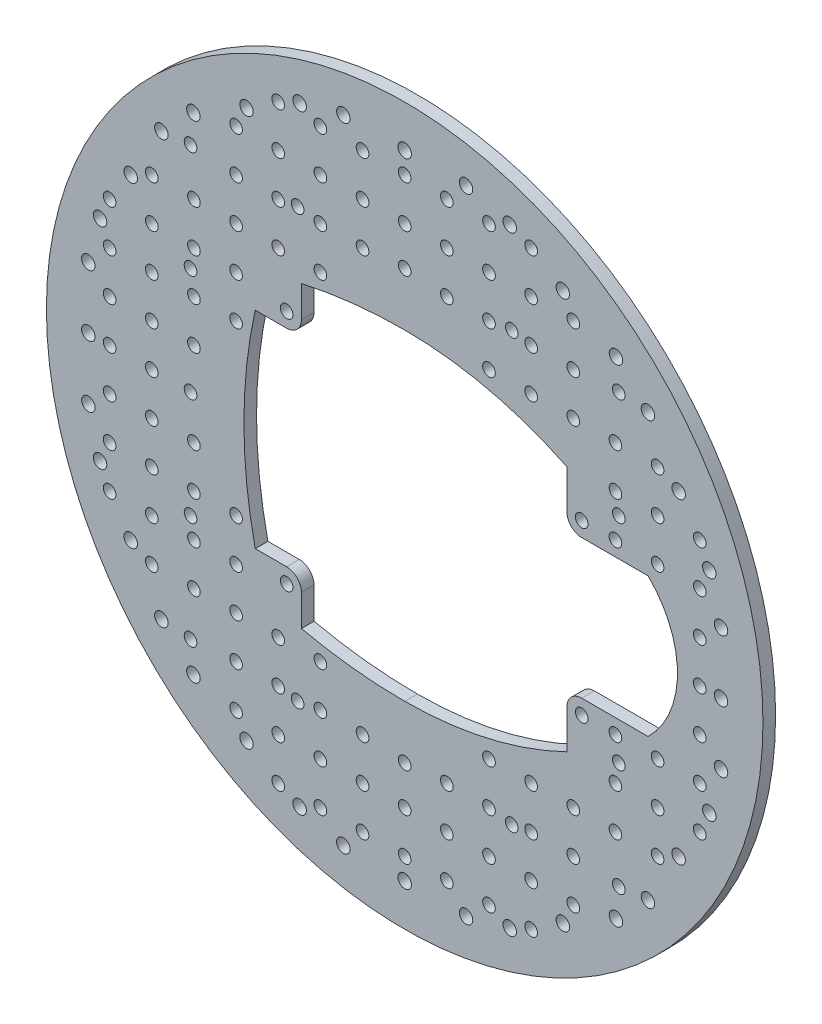
SolidWorks part; units mm, degrees
material "ABS"
ref_plane "Спереди" through (0, 0, 0) normal (0, 0, 1) x (1, 0, 0)
ref_plane "Сверху" through (0, 0, 0) normal (0, 1, 0) x (1, 0, 0)
ref_plane "Справа" through (0, 0, 0) normal (1, 0, 0) x (0, 0, -1)
sketch "Model" plane through (0, 0, 0) normal (0, 0, 1) x (1, 0, 0)
  line L0 (0, 0) -> (0, -87) construction
  line L1 (0, 0) -> (0, 87) construction
  line L2 (0, 0) -> (87, 0) construction
  line L3 (0, 0) -> (-87, 0) construction
  line L4 (38.5, 20) -> (38.5, 29.277)
  line L5 (42, 16.5) -> (57.7426, 16.5)
  line L6 (-24.5, 28) -> (-24.5, 35.4475)
  line L7 (-28, 24.5) -> (-35.4475, 24.5)
  line L8 (38.5, -20) -> (38.5, -29.277)
  line L9 (42, -16.5) -> (57.7426, -16.5)
  line L10 (-24.5, -28) -> (-24.5, -35.4475)
  line L11 (-28, -24.5) -> (-35.4475, -24.5)
  circle A295 centre (37.525, 64.9952) radius 1.6
  circle A296 centre (-50.1257, -57.7202) radius 1.6
  circle A297 centre (-57.7202, 50.1257) radius 1.6
  circle A298 centre (-24.9243, 72.2702) radius 1.6
  circle A299 centre (-75.05, 0) radius 1.6
  circle A300 centre (50.1257, -57.7202) radius 1.6
  circle A301 centre (-72.2702, 24.9243) radius 1.6
  circle A302 centre (64.9952, -37.525) radius 1.6
  circle A303 centre (50.1257, 57.7202) radius 1.6
  circle A304 centre (37.525, -64.9952) radius 1.6
  circle A305 centre (-14.55, 75.05) radius 1.6
  circle A306 centre (-72.2702, -24.9243) radius 1.6
  circle A307 centre (24.9243, -72.2702) radius 1.6
  circle A308 centre (14.55, -75.05) radius 1.6
  circle A309 centre (64.9952, 37.525) radius 1.6
  circle A310 centre (-37.525, -64.9952) radius 1.6
  circle A311 centre (-75.05, 14.55) radius 1.6
  circle A312 centre (72.2702, 24.9243) radius 1.6
  circle A313 centre (0, -75.05) radius 1.6
  circle A314 centre (-75.05, -14.55) radius 1.6
  circle A315 centre (-64.9952, 37.525) radius 1.6
  circle A316 centre (-57.7202, -50.1257) radius 1.6
  circle A317 centre (57.7202, 50.1257) radius 1.6
  circle A318 centre (-14.55, -75.05) radius 1.6
  circle A319 centre (75.05, 14.55) radius 1.6
  circle A320 centre (0, 0) radius 85
  circle A321 centre (24.9243, 72.2702) radius 1.6
  circle A322 centre (-50.1257, 57.7202) radius 1.6
  circle A323 centre (-24.9243, -72.2702) radius 1.6
  circle A324 centre (-64.9952, -37.525) radius 1.6
  circle A325 centre (75.05, -14.55) radius 1.6
  circle A326 centre (14.55, 75.05) radius 1.6
  circle A327 centre (0, 75.05) radius 1.6
  circle A328 centre (57.7202, -50.1257) radius 1.6
  circle A329 centre (75.05, 0) radius 1.6
  circle A330 centre (72.2702, -24.9243) radius 1.6
  circle A331 centre (-37.525, 64.9952) radius 1.6
  circle A332 centre (50.8, 25.4) radius 1.5
  circle A333 centre (0, 50.8) radius 1.5
  circle A334 centre (25.4, 50.8) radius 1.5
  circle A335 centre (50.8, 50.8) radius 1.5
  circle A336 centre (50.8, -25.4) radius 1.5
  circle A337 centre (0, -50.8) radius 1.5
  circle A338 centre (25.4, -50.8) radius 1.5
  circle A339 centre (50.8, -50.8) radius 1.5
  circle A340 centre (50.8, -25.4) radius 1.5
  circle A341 centre (0, -50.8) radius 1.5
  circle A342 centre (25.4, -50.8) radius 1.5
  circle A343 centre (50.8, -50.8) radius 1.5
  circle A344 centre (-50.8, 0) radius 1.5
  circle A345 centre (-50.8, 25.4) radius 1.5
  circle A346 centre (0, 50.8) radius 1.5
  circle A347 centre (-25.4, 50.8) radius 1.5
  circle A348 centre (-50.8, 50.8) radius 1.5
  circle A349 centre (-50.8, -25.4) radius 1.5
  circle A350 centre (0, -50.8) radius 1.5
  circle A351 centre (-25.4, -50.8) radius 1.5
  circle A352 centre (-50.8, -50.8) radius 1.5
  circle A353 centre (-50.8, -25.4) radius 1.5
  circle A354 centre (0, -50.8) radius 1.5
  circle A355 centre (-25.4, -50.8) radius 1.5
  circle A356 centre (-50.8, -50.8) radius 1.5
  circle A357 centre (-50.8, 0) radius 1.5
  circle A358 centre (-50.8, 25.4) radius 1.5
  circle A359 centre (0, 50.8) radius 1.5
  circle A360 centre (-25.4, 50.8) radius 1.5
  circle A361 centre (-50.8, 50.8) radius 1.5
  circle A362 centre (-50.8, -25.4) radius 1.5
  circle A363 centre (0, -50.8) radius 1.5
  circle A364 centre (-25.4, -50.8) radius 1.5
  circle A365 centre (-50.8, -50.8) radius 1.5
  circle A366 centre (-50.8, -25.4) radius 1.5
  circle A367 centre (0, -50.8) radius 1.5
  circle A368 centre (-25.4, -50.8) radius 1.5
  circle A369 centre (-50.8, -50.8) radius 1.5
  circle A370 centre (42, 20) radius 1.5
  circle A371 centre (-28, 28) radius 1.5
  arc A372 (0, 38.1403) -> (-24.5, 35.4475) centre (0, -74.6583) ccw
  arc A373 (38.5, 29.277) -> (0, 38.1403) centre (0, -49.9083) ccw
  arc A374 (64.7192, 0) -> (57.7426, 16.5) centre (41.7192, 0) ccw
  arc A375 (38.5, 20) -> (42, 16.5) centre (42, 20) ccw
  arc A376 (-28, 24.5) -> (-24.5, 28) centre (-28, 28) ccw
  arc A377 (-35.4475, 24.5) -> (-38.1403, 0) centre (74.6583, 0) ccw
  circle A378 centre (42, -20) radius 1.5
  circle A379 centre (-28, -28) radius 1.5
  arc A380 (-24.5, -35.4475) -> (0, -38.1403) centre (0, 74.6583) ccw
  arc A381 (0, -38.1403) -> (38.5, -29.277) centre (0, 49.9083) ccw
  arc A382 (57.7426, -16.5) -> (64.7192, 0) centre (41.7192, 0) ccw
  arc A383 (42, -16.5) -> (38.5, -20) centre (42, -20) ccw
  arc A384 (-24.5, -28) -> (-28, -24.5) centre (-28, -28) ccw
  arc A385 (-38.1403, 0) -> (-35.4475, -24.5) centre (74.6583, 0) ccw
  circle A386 centre (-10, 50) radius 1.5
  circle A387 centre (-10, 60) radius 1.5
  circle A388 centre (-10, 70) radius 1.5
  circle A389 centre (0, 60) radius 1.5
  circle A390 centre (0, 70) radius 1.5
  circle A391 centre (-20, 40) radius 1.5
  circle A392 centre (-20, 50) radius 1.5
  circle A393 centre (-20, 60) radius 1.5
  circle A394 centre (-20, 70) radius 1.5
  circle A395 centre (-30, 40) radius 1.5
  circle A396 centre (-30, 50) radius 1.5
  circle A397 centre (-30, 60) radius 1.5
  circle A398 centre (-30, 70) radius 1.5
  circle A399 centre (-40, 20) radius 1.5
  circle A400 centre (-40, 30) radius 1.5
  circle A401 centre (-40, 40) radius 1.5
  circle A402 centre (-40, 50) radius 1.5
  circle A403 centre (-40, 60) radius 1.5
  circle A404 centre (-50, 10) radius 1.5
  circle A405 centre (-50, 20) radius 1.5
  circle A406 centre (-50, 30) radius 1.5
  circle A407 centre (-50, 40) radius 1.5
  circle A408 centre (-60, 0) radius 1.5
  circle A409 centre (-60, 10) radius 1.5
  circle A410 centre (-60, 20) radius 1.5
  circle A411 centre (-60, 40) radius 1.5
  circle A412 centre (-70, 0) radius 1.5
  circle A413 centre (-70, 10) radius 1.5
  circle A414 centre (-70, 20) radius 1.5
  circle A415 centre (-70, 30) radius 1.5
  circle A416 centre (10, 50) radius 1.5
  circle A417 centre (10, 60) radius 1.5
  circle A418 centre (10, 70) radius 1.5
  circle A419 centre (20, 40) radius 1.5
  circle A420 centre (20, 50) radius 1.5
  circle A421 centre (20, 60) radius 1.5
  circle A422 centre (20, 70) radius 1.5
  circle A423 centre (30, 40) radius 1.5
  circle A424 centre (30, 50) radius 1.5
  circle A425 centre (30, 60) radius 1.5
  circle A426 centre (30, 70) radius 1.5
  circle A427 centre (40, 40) radius 1.5
  circle A428 centre (40, 50) radius 1.5
  circle A429 centre (40, 60) radius 1.5
  circle A430 centre (50, 20) radius 1.5
  circle A431 centre (50, 30) radius 1.5
  circle A432 centre (50, 40) radius 1.5
  circle A433 centre (60, 20) radius 1.5
  circle A434 centre (60, 30) radius 1.5
  circle A435 centre (60, 40) radius 1.5
  circle A436 centre (70, 10) radius 1.5
  circle A437 centre (70, 20) radius 1.5
  circle A438 centre (70, 30) radius 1.5
  circle A439 centre (70, 0) radius 1.5
  circle A440 centre (-10, -50) radius 1.5
  circle A441 centre (-10, -60) radius 1.5
  circle A442 centre (-10, -70) radius 1.5
  circle A443 centre (0, -60) radius 1.5
  circle A444 centre (0, -70) radius 1.5
  circle A445 centre (-20, -40) radius 1.5
  circle A446 centre (-20, -50) radius 1.5
  circle A447 centre (-20, -60) radius 1.5
  circle A448 centre (-20, -70) radius 1.5
  circle A449 centre (-30, -40) radius 1.5
  circle A450 centre (-30, -50) radius 1.5
  circle A451 centre (-30, -60) radius 1.5
  circle A452 centre (-30, -70) radius 1.5
  circle A453 centre (-40, -20) radius 1.5
  circle A454 centre (-40, -30) radius 1.5
  circle A455 centre (-40, -40) radius 1.5
  circle A456 centre (-40, -50) radius 1.5
  circle A457 centre (-40, -60) radius 1.5
  circle A458 centre (-50, -10) radius 1.5
  circle A459 centre (-50, -20) radius 1.5
  circle A460 centre (-50, -30) radius 1.5
  circle A461 centre (-50, -40) radius 1.5
  circle A462 centre (-60, -10) radius 1.5
  circle A463 centre (-60, -20) radius 1.5
  circle A464 centre (-60, -40) radius 1.5
  circle A465 centre (-70, -10) radius 1.5
  circle A466 centre (-70, -20) radius 1.5
  circle A467 centre (-70, -30) radius 1.5
  circle A468 centre (10, -50) radius 1.5
  circle A469 centre (10, -60) radius 1.5
  circle A470 centre (10, -70) radius 1.5
  circle A471 centre (20, -40) radius 1.5
  circle A472 centre (20, -50) radius 1.5
  circle A473 centre (20, -60) radius 1.5
  circle A474 centre (20, -70) radius 1.5
  circle A475 centre (30, -40) radius 1.5
  circle A476 centre (30, -50) radius 1.5
  circle A477 centre (30, -60) radius 1.5
  circle A478 centre (30, -70) radius 1.5
  circle A479 centre (40, -40) radius 1.5
  circle A480 centre (40, -50) radius 1.5
  circle A481 centre (40, -60) radius 1.5
  circle A482 centre (50, -20) radius 1.5
  circle A483 centre (50, -30) radius 1.5
  circle A484 centre (50, -40) radius 1.5
  circle A485 centre (60, -20) radius 1.5
  circle A486 centre (60, -30) radius 1.5
  circle A487 centre (60, -40) radius 1.5
  circle A488 centre (70, -10) radius 1.5
  circle A489 centre (70, -20) radius 1.5
  circle A490 centre (70, -30) radius 1.5
  circle A491 centre (-60, 30) radius 1.5
  circle A492 centre (-60, -30) radius 1.5
extrude "Бобышка-Вытянуть1" add sketch "Model" along normal blind 3
